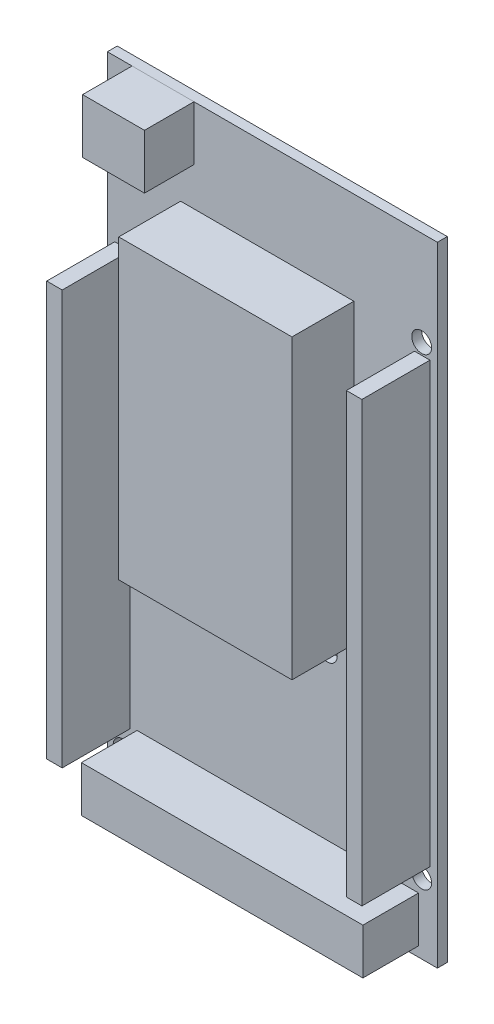
SolidWorks part; units mm, degrees
ref_plane "前基準面" through (0, 0, 0) normal (0, 0, 1) x (1, 0, 0)
ref_plane "上基準面" through (0, 0, 0) normal (0, 1, 0) x (1, 0, 0)
ref_plane "右基準面" through (0, 0, 0) normal (1, 0, 0) x (0, 0, -1)
sketch "草圖1" plane through (0, 0, 0) normal (0, 0, 1) x (1, 0, 0)
  line L1 (26.67, -50.8) -> (-26.67, -50.8)
  line L2 (26.67, -50.8) -> (26.67, 50.8)
  line L3 (26.67, 50.8) -> (-26.67, 50.8)
  line L4 (-26.67, -50.8) -> (-26.67, 50.8)
  line L5 (26.67, -50.8) -> (-26.67, 50.8) construction
  line L6 (26.67, 50.8) -> (-26.67, -50.8) construction
  point P0 (0, 0)
  dimension "D1" = 53.34
  dimension "D2" = 101.6
extrude "填料-伸長1" add sketch "草圖1" along normal blind 1.6
sketch "草圖2" plane through (0, 0, 1.6) normal (0, 0, 1) x (1, 0, 0)
  line L0 (26.67, -50.8) -> (26.67, 50.8) construction
  line L1 (-25.47, 24.8) -> (-22.97, 24.8)
  line L2 (-25.47, 24.8) -> (-25.47, -42.1)
  line L3 (-25.47, -42.1) -> (-22.97, -42.1)
  line L4 (-22.97, 24.8) -> (-22.97, -42.1)
  line L5 (25.47, 33.7) -> (22.97, 33.7)
  line L6 (25.47, 33.7) -> (25.47, -37.2)
  line L7 (25.47, -37.2) -> (22.97, -37.2)
  line L8 (22.97, 33.7) -> (22.97, -37.2)
  line L9 (-26.67, 50.8) -> (-26.67, -50.8) construction
  line L10 (-26.67, -50.8) -> (26.67, -50.8) construction
  dimension "D1" = 2.5
  dimension "D2" = 1.2
  dimension "D3" = 1.2
  dimension "D4" = 70.9
  dimension "D5" = 66.9
  dimension "D6" = 13.6
  dimension "D7" = 8.7
extrude "填料-伸長2" add sketch "草圖2" along normal blind 11
sketch "草圖3" plane through (0, 0, 1.6) normal (0, 0, 1) x (1, 0, 0)
  line L0 (-26.67, -50.8) -> (26.67, -50.8) construction
  line L1 (-21.87, -41.8) -> (23.63, -41.8)
  line L2 (-21.87, -41.8) -> (-21.87, -49.2)
  line L3 (-21.87, -49.2) -> (23.63, -49.2)
  line L4 (23.63, -41.8) -> (23.63, -49.2)
  line L5 (-26.67, 50.8) -> (-26.67, -50.8) construction
  dimension "D1" = 1.6
  dimension "D2" = 7.4
  dimension "D3" = 45.5
  dimension "D4" = 4.8
extrude "填料-伸長3" add sketch "草圖3" along normal blind 9
hole_wizard "Ø3.2 (3.2) 直徑孔1" positions "草圖4" profile "草圖6" hole size "Ø3.2" standard "ISO" end condition up to next
sketch "草圖4" plane through (0, 0, 1.6) normal (0, 0, 1) x (1, 0, 0)
  line L2 (26.67, 50.8) -> (-26.67, 50.8) construction
  line L3 (-26.67, 50.8) -> (-26.67, -50.8) construction
  point P0 (24.13, -39.37)
  point P2 (-24.13, -45.72)
  point P4 (-19.05, -15.24)
  point P6 (8.89, -15.24)
  point P8 (-24.13, 36.83)
  point P10 (24.13, 35.56)
  dimension "D1" = 13.97
  dimension "D2" = 15.24
  dimension "D3" = 90.17
  dimension "D4" = 66.04
  dimension "D5" = 66.04
  dimension "D6" = 96.52
  dimension "D7" = 2.54
  dimension "D8" = 50.8
  dimension "D9" = 7.62
  dimension "D10" = 35.56
  dimension "D11" = 2.54
  dimension "D12" = 50.8
sketch "草圖6" plane through (24.13, -39.37, 1.6) normal (1, 0, 0) x (0, -1, 0)
  line L0 (0, 0) -> (0, 1.6)
  line L1 (0, 1.6) -> (1.6, 1.6)
  line L2 (1.6, 1.6) -> (1.6, 0)
  line L5 (1.6, 0) -> (0, 0)
  line L11 (0, -6.35) -> (0, 107.95) construction
  dimension "貫穿孔直徑" = 3.2
  dimension "貫穿孔深度" = 1.6
sketch "草圖7" plane through (0, 0, 1.6) normal (0, 0, 1) x (1, 0, 0)
  line L0 (-26.67, -50.8) -> (26.67, -50.8) construction
  line L1 (-14.83, 35.8) -> (13.17, 35.8)
  line L2 (-14.83, 35.8) -> (-14.83, -12.2)
  line L3 (-14.83, -12.2) -> (13.17, -12.2)
  line L4 (13.17, 35.8) -> (13.17, -12.2)
  line L5 (26.67, -50.8) -> (26.67, 50.8) construction
  dimension "D1" = 28
  dimension "D2" = 48
  dimension "D3" = 86.6
  dimension "D4" = 41.5
extrude "填料-伸長4" add sketch "草圖7" along normal blind 10
sketch "草圖8" plane through (0, 0, 1.6) normal (0, 0, 1) x (1, 0, 0)
  line L0 (26.67, 50.8) -> (-26.67, 50.8) construction
  line L1 (-12.67, 50.8) -> (-22.67, 50.8)
  line L2 (-12.67, 50.8) -> (-12.67, 42)
  line L3 (-12.67, 42) -> (-22.67, 42)
  line L4 (-22.67, 50.8) -> (-22.67, 42)
  line L5 (-26.67, 50.8) -> (-26.67, -50.8) construction
  dimension "D1" = 10
  dimension "D2" = 8.8
  dimension "D3" = 4
extrude "填料-伸長5" add sketch "草圖8" along normal blind 8 separate body
